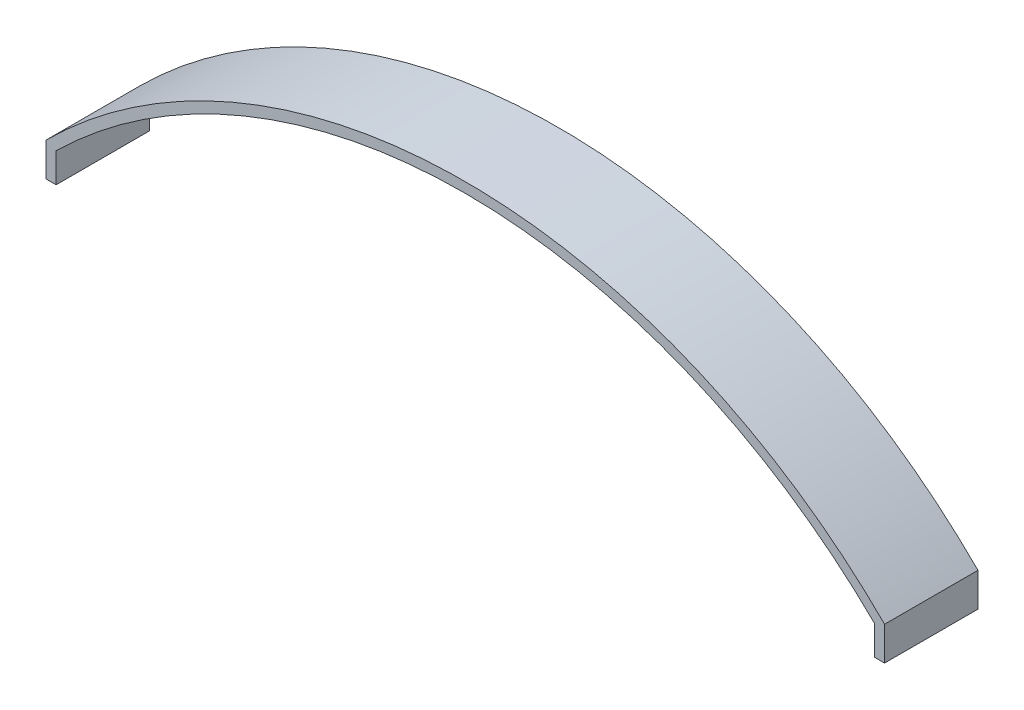
SolidWorks part; units mm, degrees
material "Velcro"
ref_plane "Front Plane" through (0, 0, 0) normal (0, 0, 1) x (1, 0, 0)
ref_plane "Top Plane" through (0, 0, 0) normal (0, 1, 0) x (1, 0, 0)
ref_plane "Right Plane" through (0, 0, 0) normal (1, 0, 0) x (0, 0, -1)
sketch "Sketch1" plane through (0, 0, 0) normal (0, 0, 1) x (1, 0, 0)
  line L0 (-182, 14.6131) -> (-182, 0)
  line L2 (182, 14.6131) -> (182, 0)
  line L3 (177.6, 12.7814) -> (177.6, 4.4)
  line L5 (-177.6, 12.7814) -> (-177.6, 4.4)
  line L6 (-177.6, 4.4) -> (177.6, 4.4) construction
  line L7 (-182, 0) -> (182, 0) construction
  line L8 (-177.6, 4.4) -> (-177.6, 0)
  line L9 (-177.6, 0) -> (-182, 0)
  line L10 (177.6, 4.4) -> (177.6, 0)
  line L11 (177.6, 0) -> (182, 0)
  arc A0 (-182, 14.6131) -> (182, 14.6131) centre (0, -167.3869) cw
  arc A1 (-177.6, 12.7814) -> (177.6, 12.7814) centre (0, -167.3869) cw
  point P3 (0, 0)
  dimension "D2" = 90
  dimension "D1" = 364
  dimension "D3" = 4.4
extrude "Boss-Extrude1" add sketch "Sketch1" against normal blind 40.56
